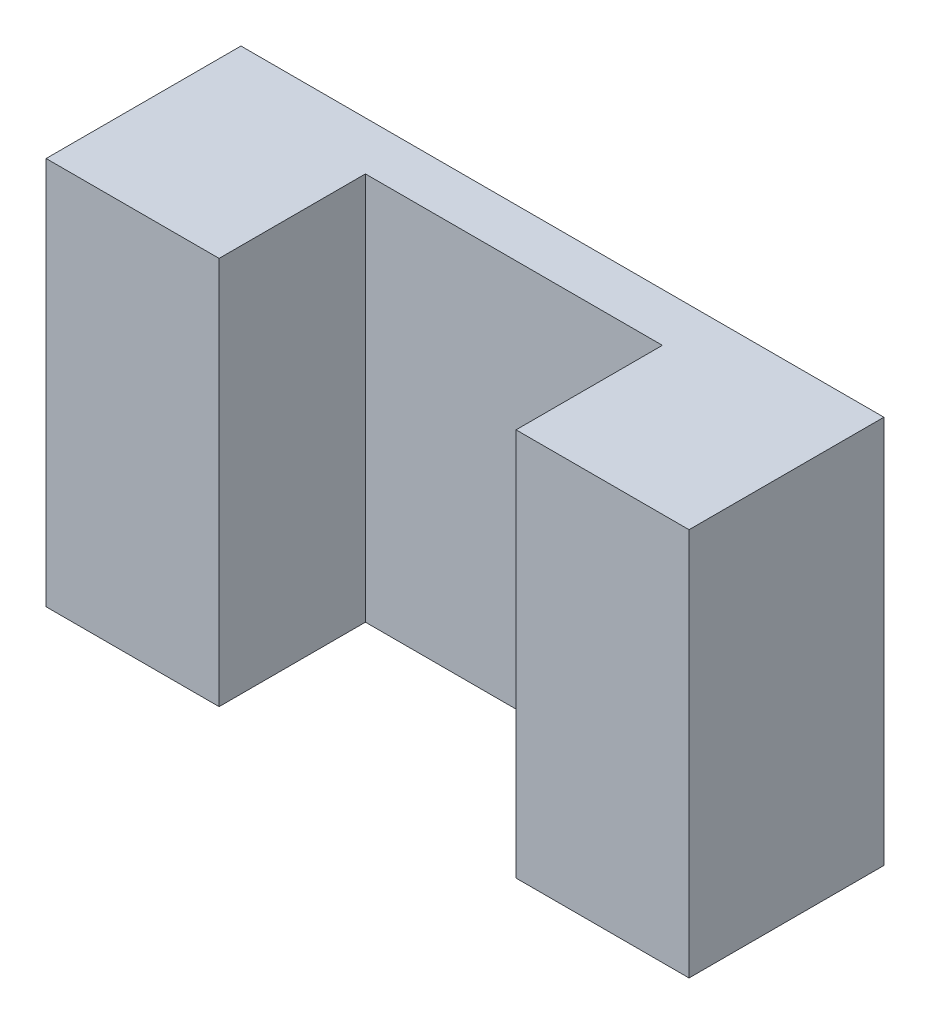
SolidWorks part; units mm, degrees
material "ABS"
ref_plane "Front Plane" through (0, 0, 0) normal (0, 0, 1) x (1, 0, 0)
ref_plane "Top Plane" through (0, 0, 0) normal (0, 1, 0) x (1, 0, 0)
ref_plane "Right Plane" through (0, 0, 0) normal (1, 0, 0) x (0, 0, -1)
sketch "Sketch1" plane through (0, 0, 0) normal (0, 0, 1) x (1, 0, 0)
  line L1 (32.9969, 19.925) -> (-32.9969, 19.925)
  line L2 (32.9969, 19.925) -> (32.9969, -19.925)
  line L3 (32.9969, -19.925) -> (-32.9969, -19.925)
  line L4 (-32.9969, 19.925) -> (-32.9969, -19.925)
  line L5 (32.9969, 19.925) -> (-32.9969, -19.925) construction
  line L6 (32.9969, -19.925) -> (-32.9969, 19.925) construction
  point P0 (0, 0)
  dimension "D1" = 39.85
  dimension "D2" = 65.9938
extrude "Boss-Extrude1" add sketch "Sketch1" along normal blind 20
sketch "Sketch2" plane through (0, 0, 20) normal (0, 0, 1) x (1, 0, 0)
  line L0 (-32.9969, -19.925) -> (32.9969, -19.925) construction
  line L1 (15.24, 19.925) -> (-15.24, 19.925)
  line L2 (15.24, 19.925) -> (15.24, -19.925)
  line L3 (15.24, -19.925) -> (-15.24, -19.925)
  line L4 (-15.24, 19.925) -> (-15.24, -19.925)
  line L5 (15.24, 19.925) -> (-15.24, -19.925) construction
  line L6 (15.24, -19.925) -> (-15.24, 19.925) construction
  point P0 (0, 0)
  dimension "D1" = 30.48
extrude "Cut-Extrude1" cut sketch "Sketch2" against normal blind 15.02
